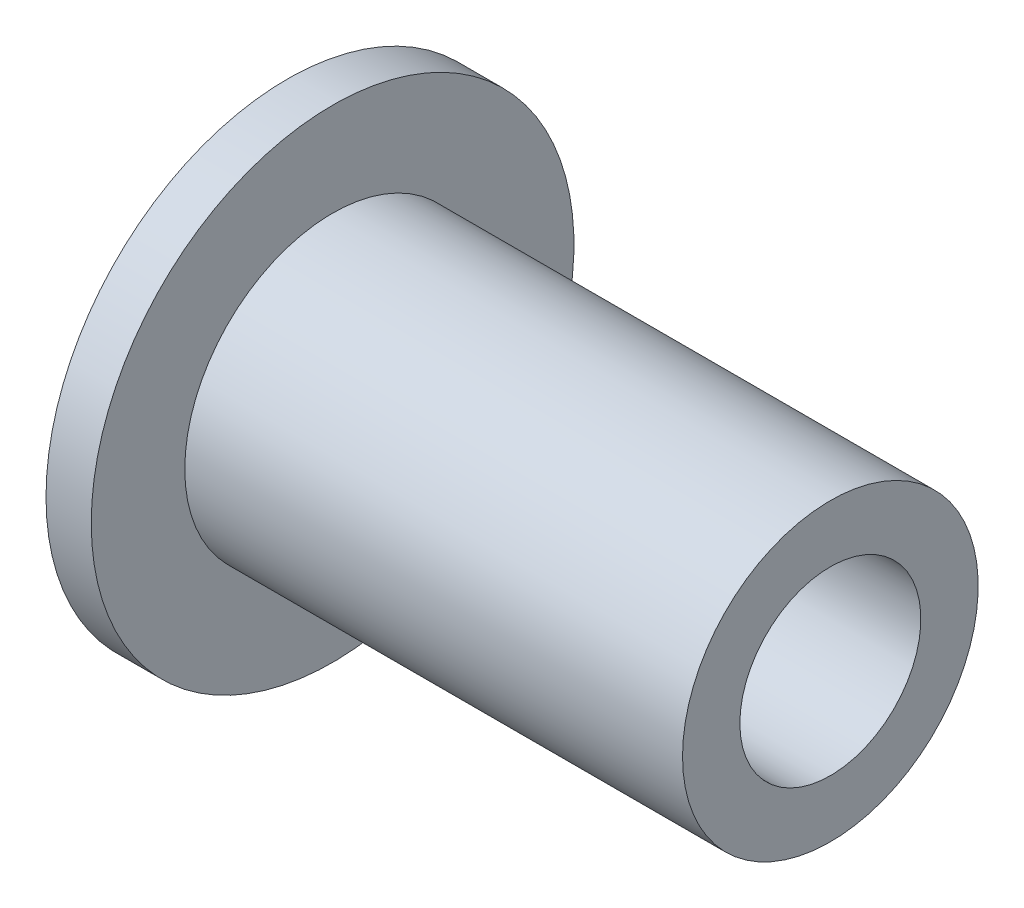
SolidWorks part; units mm, degrees
material "1060 合金"
ref_plane "前视基准面" through (0, 0, 0) normal (0, 0, 1) x (1, 0, 0)
ref_plane "上视基准面" through (0, 0, 0) normal (0, 1, 0) x (1, 0, 0)
ref_plane "右视基准面" through (0, 0, 0) normal (1, 0, 0) x (0, 0, -1)
other "Configuration Table"
sketch "草图1" plane through (0, 0, 0) normal (0, 0, 1) x (1, 0, 0)
  line L0 (0, 0) -> (2770.6685, 0) construction
  line L1 (0, 0) -> (0, 1.9) construction
  line L2 (0, 1.9) -> (0, 4)
  line L3 (0, 4) -> (0.75, 4)
  line L4 (0.75, 4) -> (0.75, 2.45)
  line L5 (0.75, 2.45) -> (9, 2.45)
  line L6 (9, 2.45) -> (9, 1.5)
  line L7 (9, 1.5) -> (4, 1.5)
  line L8 (4, 1.5) -> (4, 1.9)
  line L9 (4, 1.9) -> (0, 1.9)
  dimension "D1" = 1.9
  dimension "D2" = 4
  dimension "D3" = 0.75
  dimension "D4" = 2.45
  dimension "D5" = 9
  dimension "D6" = 1.5
  dimension "D7" = 5
revolve "旋转1" add sketch "草图1" angle 360 about L0
